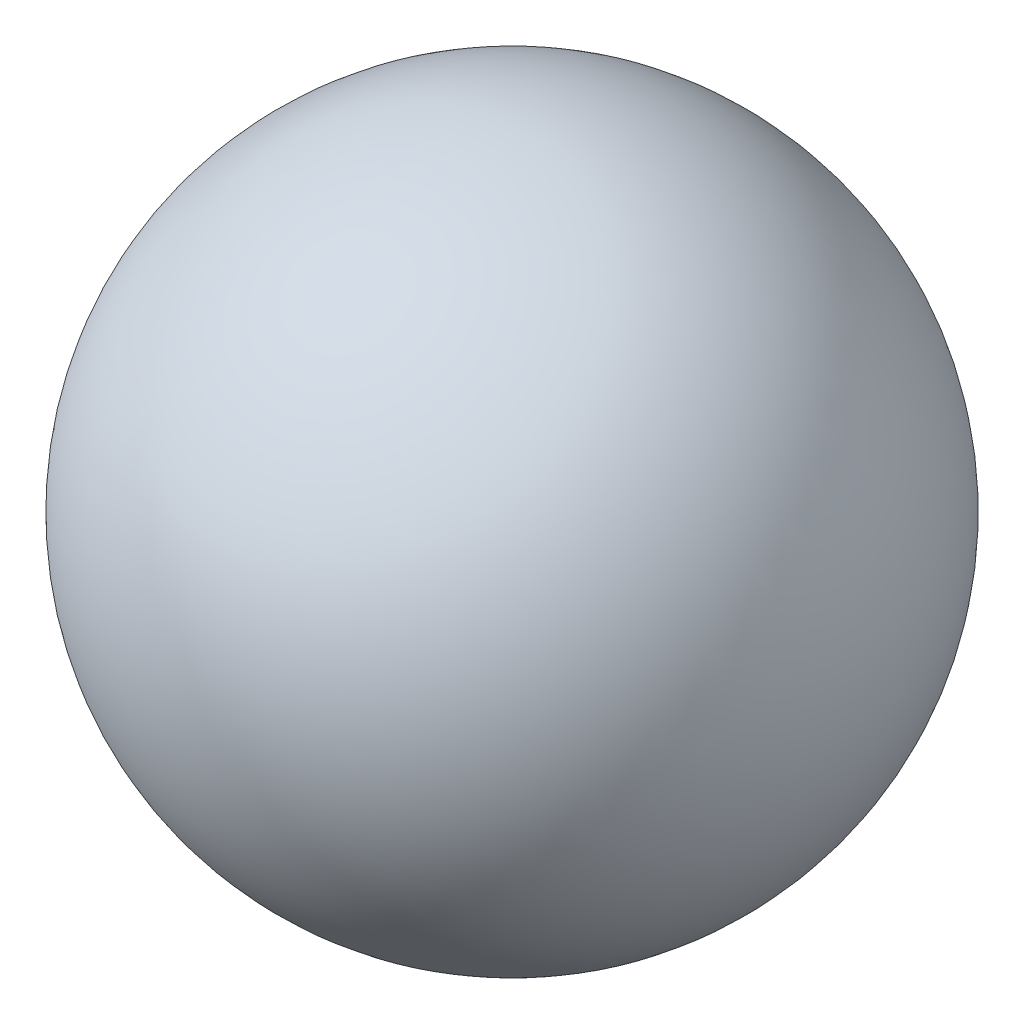
SolidWorks part; units mm, degrees
ref_plane "Ebene vorne" through (0, 0, 0) normal (0, 0, 1) x (1, 0, 0)
ref_plane "Ebene oben" through (0, 0, 0) normal (0, 1, 0) x (1, 0, 0)
ref_plane "Ebene rechts" through (0, 0, 0) normal (1, 0, 0) x (0, 0, -1)
sketch "Skizze1" plane through (0, 0, 0) normal (0, 0, 1) x (1, 0, 0)
  line L0 (0, 120) -> (0, -120)
  arc A0 (0, 120) -> (0, -120) centre (0, 0) cw
  point P2 (0, 0)
  dimension "D1" = 240
revolve "Rotation1" add sketch "Skizze1" angle 360 about L0
